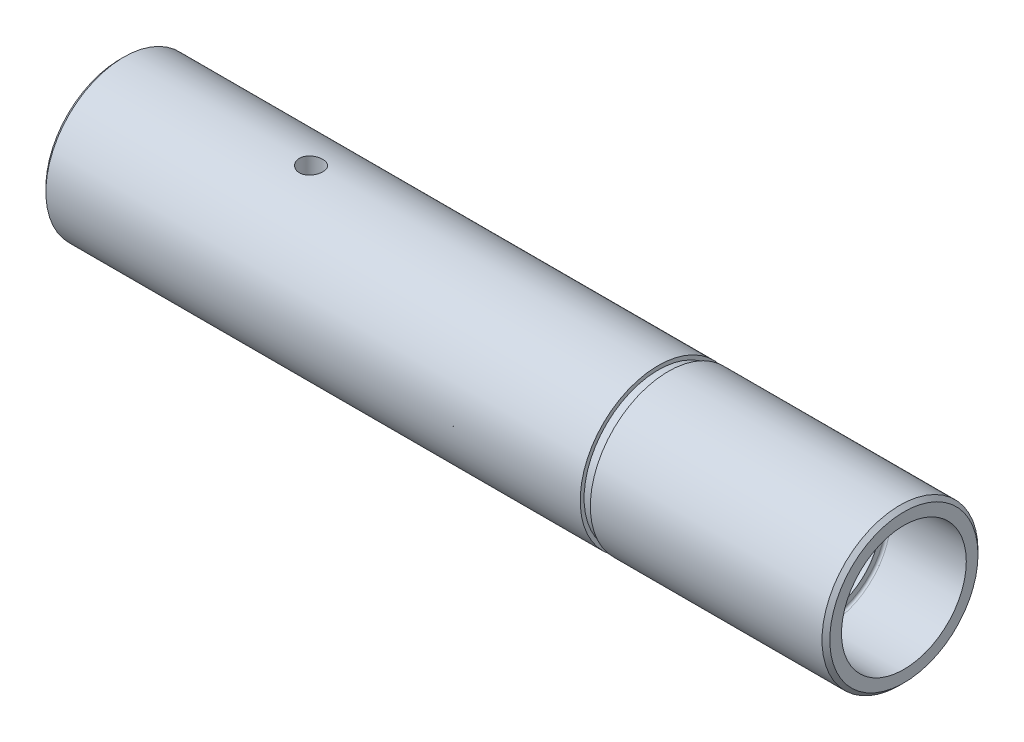
SolidWorks part; units mm, degrees
material "Stainless Steel (ferritic)"
ref_plane "Front Plane" through (0, 0, 0) normal (0, 0, 1) x (1, 0, 0)
ref_plane "Top Plane" through (0, 0, 0) normal (0, 1, 0) x (1, 0, 0)
ref_plane "Right Plane" through (0, 0, 0) normal (1, 0, 0) x (0, 0, -1)
sketch "Sketch1" plane through (0, 0, 0) normal (1, 0, 0) x (0, 0, -1)
  circle A0 centre (0, 0) radius 7
  circle A1 centre (0, 0) radius 10
  dimension "D1" = 20
  dimension "D2" = 3
extrude "Boss-Extrude1" add sketch "Sketch1" along normal blind 100.5
sketch "Sketch2" plane through (0, 0, 0) normal (-1, 0, 0) x (0, 0, 1)
  circle A0 centre (0, 0) radius 8
  dimension "D1" = 16
extrude "Cut-Extrude1" cut sketch "Sketch2" against normal blind 10
sketch "Sketch3" plane through (100.5, 0, 0) normal (1, 0, 0) x (0, 0, -1)
  circle A0 centre (0, 0) radius 8
  dimension "D1" = 16
extrude "Cut-Extrude2" cut sketch "Sketch3" against normal blind 10
sketch "Sketch4" plane through (0, 0, 0) normal (0, 0, 1) x (1, 0, 0)
  line L0 (69, 10) -> (69, 9.5)
  line L1 (100.5, 10) -> (0, 10) construction
  line L2 (69, 9.5) -> (70.3, 9.5)
  line L3 (70.3, 9.5) -> (70.3, 10)
  line L4 (70.3, 10) -> (69, 10)
  line L6 (0, 10) -> (0, -10) construction
  dimension "D1" = 69
  dimension "D2" = 1.3
  dimension "D3" = 0.5
ref_axis "Axis1" through (100.5, 0, 0) along (-1, 0, 0)
revolve "Cut-Revolve1" cut sketch "Sketch4" angle 360 about axis through (100.5, 0, 0) along (-1, 0, 0)
sketch "Sketch5" plane through (0, 0, 0) normal (0, 1, 0) x (1, 0, 0)
  line L0 (100.5, 0) -> (0, 0) construction
  circle A0 centre (24.5, 0) radius 1.5
  dimension "D1" = 3
  dimension "D2" = 24.5
extrude "Cut-Extrude3" cut sketch "Sketch5" against normal mid plane 20
chamfer "Chamfer1" distance 0.5 angle 45 2 edges at (0, 0, -10) (100.5, 0, -10)
fillet "Fillet1" radius 0.3 2 edges at (90.5, 0, -8) (10, 0, 8)
